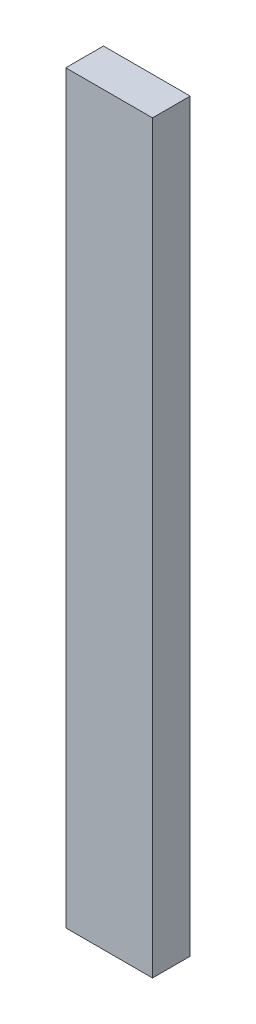
SolidWorks part; units mm, degrees
material "Pine"
ref_plane "Front Plane" through (0, 0, 0) normal (0, 0, 1) x (1, 0, 0)
ref_plane "Top Plane" through (0, 0, 0) normal (0, 1, 0) x (1, 0, 0)
ref_plane "Right Plane" through (0, 0, 0) normal (1, 0, 0) x (0, 0, -1)
sketch "Sketch1" plane through (0, 0, 0) normal (0, 1, 0) x (1, 0, 0)
  line L1 (-23, -10) -> (23, -10)
  line L2 (-23, -10) -> (-23, 10)
  line L3 (-23, 10) -> (23, 10)
  line L4 (23, -10) -> (23, 10)
  line L5 (-23, -10) -> (23, 10) construction
  line L6 (-23, 10) -> (23, -10) construction
  point P0 (0, 0)
  dimension "D1" = 46
  dimension "D2" = 20
extrude "Boss-Extrude1" add sketch "Sketch1" along normal blind 395
